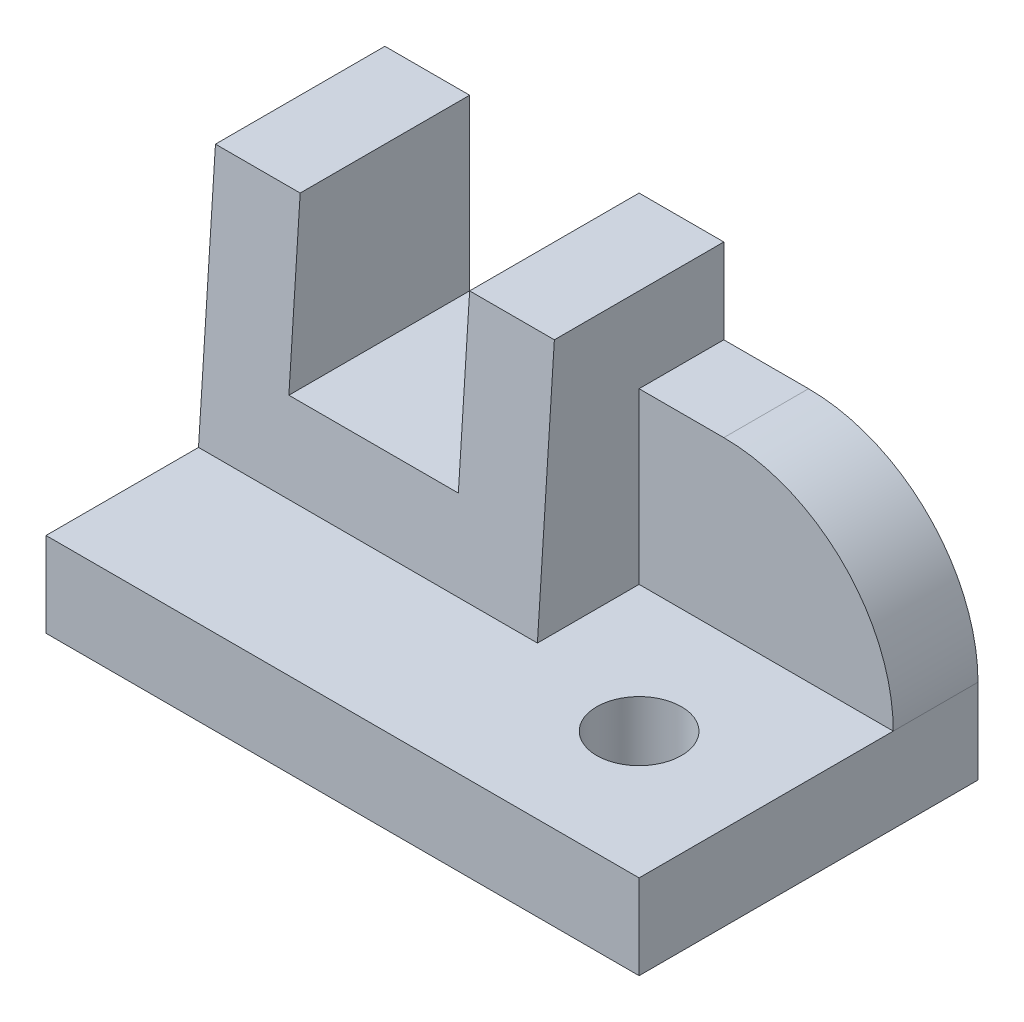
SolidWorks part; units mm, degrees
ref_plane "Front Plane" through (0, 0, 0) normal (0, 0, 1) x (1, 0, 0)
ref_plane "Top Plane" through (0, 0, 0) normal (0, 1, 0) x (1, 0, 0)
ref_plane "Right Plane" through (0, 0, 0) normal (1, 0, 0) x (0, 0, -1)
ref_plane "Plane1" through (0, 0, 0) normal (-1, 0, 0) x (0, -1, 0)
sketch "Sketch1" plane through (0, 0, 0) normal (-1, 0, 0) x (0, -1, 0)
  line L0 (-10, -18) -> (-40, -20)
  line L1 (-40, -20) -> (-10, -20)
  line L2 (-10, -20) -> (-10, -18)
  dimension "D1" = 30
  dimension "Width" = 2
extrude "Boss-Extrude1" add sketch "Sketch1" against normal blind 40
sketch "Sketch2" plane through (0, 0, -20) normal (0, 0, -1) x (-1, 0, 0)
  line L0 (-40, 40) -> (0, 40)
  line L1 (0, 40) -> (0, 10)
  line L2 (0, 10) -> (-40, 10)
  line L3 (-40, 10) -> (-40, 40)
extrude "Boss-Extrude2" add sketch "Sketch2" along normal blind 20
sketch "Sketch3" plane through (40, 0, 0) normal (1, 0, 0) x (0, 0, -1)
  line L0 (40, 10) -> (0, 10)
  line L1 (0, 10) -> (20, 40)
  line L2 (20, 40) -> (40, 40)
  line L3 (40, 40) -> (40, 10)
extrude "Boss-Extrude3" add sketch "Sketch3" along normal blind 30
sketch "Sketch4" plane through (70, 0, 0) normal (1, 0, 0) x (0, 0, -1)
  line L0 (20, 40) -> (0, 10)
  line L1 (0, 10) -> (30, 10)
  line L2 (30, 10) -> (30, 30)
  line L3 (30, 30) -> (40, 30)
  line L4 (40, 30) -> (40, 40)
  line L5 (40, 40) -> (20, 40)
extrude "Cut-Extrude1" cut sketch "Sketch4" against normal blind 30
sketch "Sketch5" plane through (0, 10, 0) normal (0, -1, 0) x (1, 0, 0)
  line L0 (70, 0) -> (70, -40)
  line L1 (70, -40) -> (0, -40)
  line L2 (0, -40) -> (0, 0)
  line L3 (0, 0) -> (70, 0)
extrude "Boss-Extrude4" add sketch "Sketch5" along normal blind 10
sketch "Sketch6" plane through (0, 0, -40) normal (0, 0, -1) x (-1, 0, 0)
  line L0 (-30, 40) -> (-30, 20)
  line L1 (-30, 20) -> (-10, 20)
  line L2 (-10, 20) -> (-10, 40)
  line L3 (-10, 40) -> (-30, 40)
extrude "Cut-Extrude2" cut sketch "Sketch6" against normal through all
hole_wizard "Ø10.0 (10) Diameter Hole1" positions "Sketch8" profile "Sketch7" hole size "Ø10.0" standard "ANSI Metric"
sketch "Sketch8" plane through (0, 0, 0) normal (0, -1, 0) x (-1, 0, 0)
  point P0 (-55, 15)
sketch "Sketch7" plane through (55, 0, -15) normal (1, 0, 0) x (0, 0, -1)
  line L0 (0, 0) -> (0, 40)
  line L1 (0, 40) -> (5, 40)
  line L2 (5, 40) -> (5, 0)
  line L5 (5, 0) -> (0, 0)
  line L11 (0, -6.35) -> (0, 107.95) construction
  dimension "Thru Hole Dia." = 10
  dimension "Thru Hole Depth" = 40
fillet "Fillet1" radius 20 1 edges at (70, 30, -35)
